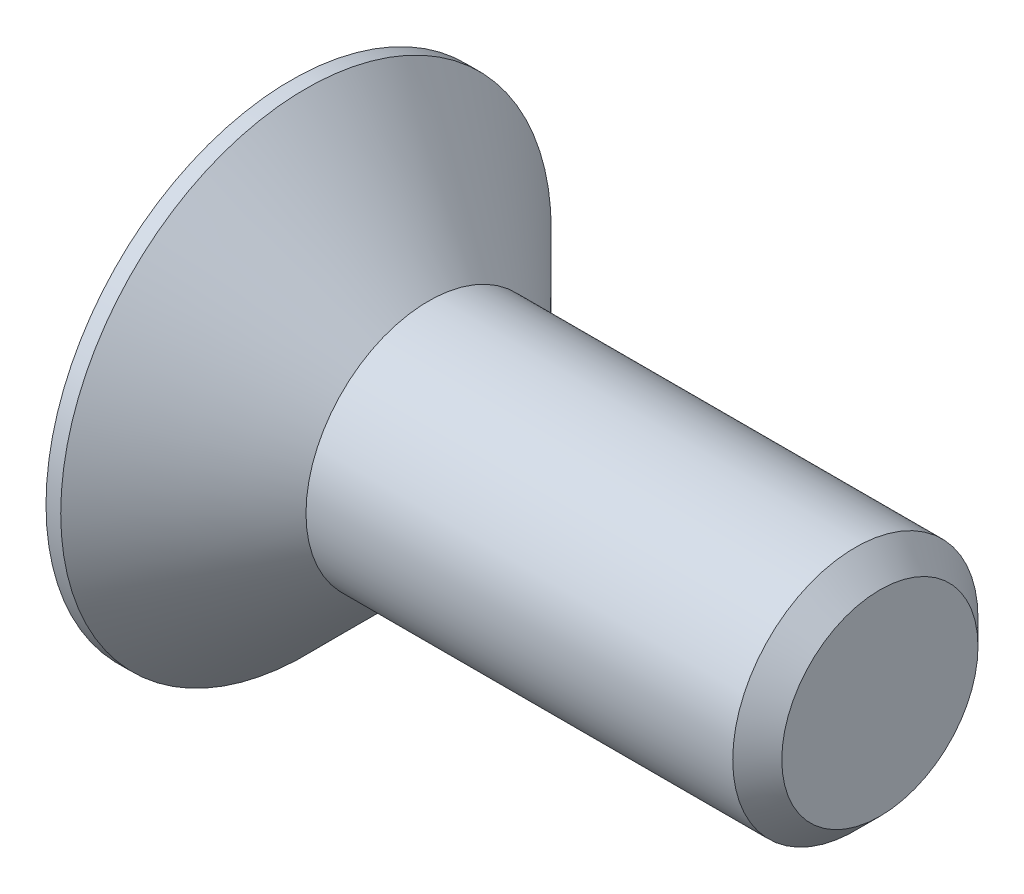
SolidWorks part; units mm, degrees
ref_plane "Front Plane" through (0, 0, 0) normal (0, 0, 1) x (1, 0, 0)
ref_plane "Top Plane" through (0, 0, 0) normal (0, 1, 0) x (1, 0, 0)
ref_plane "Right Plane" through (0, 0, 0) normal (1, 0, 0) x (0, 0, -1)
sketch "Sketch2" plane through (0, 0, 0) normal (0, 0, 1) x (1, 0, 0)
  line L0 (0, 0) -> (0, 2.5)
  line L1 (0, 2.5) -> (0.15, 2.5)
  line L2 (0.15, 2.5) -> (1.4, 1.25)
  line L3 (1.4, 1.25) -> (5.75, 1.25)
  line L4 (5.75, 1.25) -> (6, 1)
  line L5 (6, 1) -> (6, 0)
  line L6 (6, 0) -> (0, 0)
  line L7 (-2.2818, 0) -> (8.0811, 0) construction
  dimension "D1" = 5
  dimension "D2" = 0.15
  dimension "D3" = 45
  dimension "D4" = 6
  dimension "D5" = 0.25
  dimension "D6" = 2.5
revolve "Revolve1" add sketch "Sketch2" angle 360 about L7
sketch "Sketch3" plane through (0, 0, 0) normal (-1, 0, 0) x (0, 0, 1)
  line L1 (0.433, -0.75) -> (0.866, 0)
  line L2 (0.866, 0) -> (0.433, 0.75)
  line L3 (0.433, 0.75) -> (-0.433, 0.75)
  line L4 (-0.433, 0.75) -> (-0.866, 0)
  line L5 (-0.866, 0) -> (-0.433, -0.75)
  line L6 (-0.433, -0.75) -> (0.433, -0.75)
  circle A0 centre (0, 0) radius 0.75 construction
  dimension "D1" = 1.5
extrude "Cut-Extrude1" cut sketch "Sketch3" against normal blind 0.8
